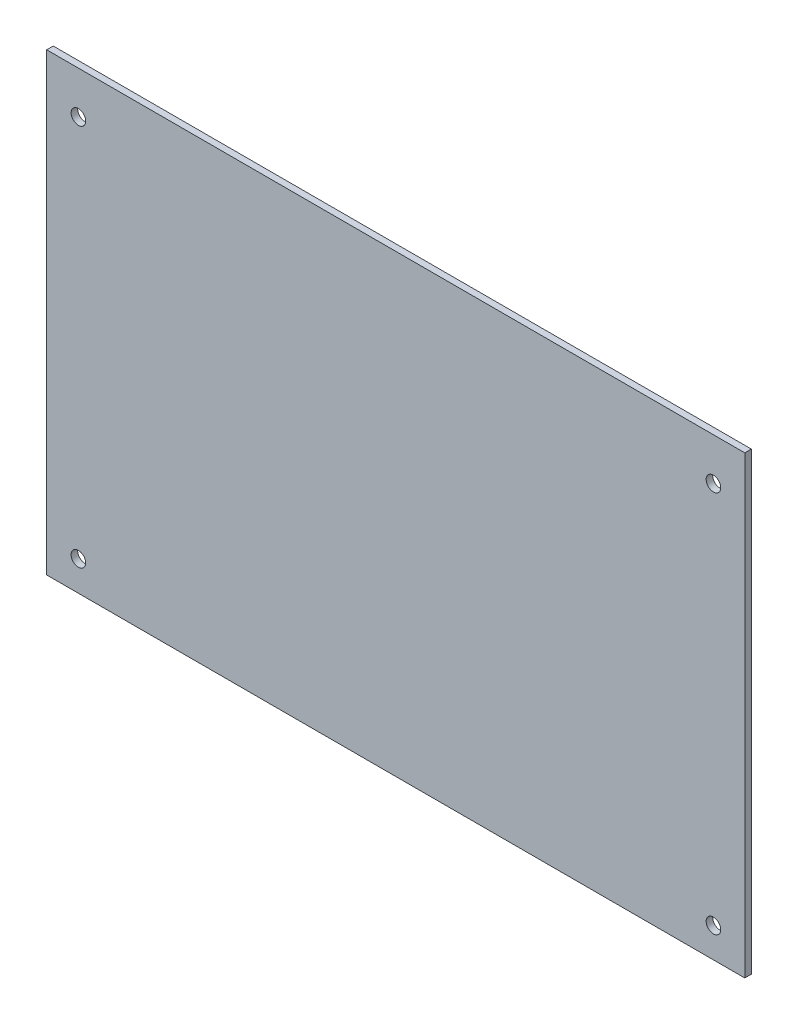
SolidWorks part; units mm, degrees
ref_plane "Front" through (0, 0, 0) normal (0, 0, 1) x (1, 0, 0)
ref_plane "Top" through (0, 0, 0) normal (0, 1, 0) x (1, 0, 0)
ref_plane "Right" through (0, 0, 0) normal (1, 0, 0) x (0, 0, -1)
sketch "Sketch1" plane through (0, 0, 0) normal (0, 0, 1) x (1, 0, 0)
  line L1 (-37.4747, 71.5987) -> (130.1653, 71.5987)
  line L2 (-37.4747, 71.5987) -> (-37.4747, -37.6213)
  line L3 (-37.4747, -37.6213) -> (130.1653, -37.6213)
  line L4 (130.1653, 71.5987) -> (130.1653, -37.6213)
  dimension "D1" = 167.64
  dimension "D2" = 109.22
extrude "PCB" add sketch "Sketch1" along normal blind 1.5748
sketch "Sketch2" plane through (0, 0, 1.5748) normal (0, 0, 1) x (1, 0, 0)
  line L0 (-37.4747, 71.5987) -> (-37.4747, -37.6213) construction
  line L1 (130.1653, 71.5987) -> (-37.4747, 71.5987) construction
  circle A0 centre (-29.8547, 61.4387) radius 1.75
  dimension "D1" = 3.5
  dimension "D2" = 7.62
  dimension "D3" = 10.16
extrude "mount hole cut" cut sketch "Sketch2" against normal blind 1.5748
pattern_linear "LPattern1" count 2 spacing 152.5 along (1, 0, 0) count 2 spacing 91.9 along (0, -1, 0) of "mount hole cut"
sketch "Sketch3" plane through (0, 0, 0) normal (0, 0, -1) x (-1, 0, 0)
  line L0 (11.0863, -1.9913) -> (3.6231, -1.9913) construction
  line L1 (3.6231, 1.0732) -> (11.0863, 1.0732)
  line L2 (3.6231, 1.0732) -> (3.6231, -5.0559)
  line L3 (3.6231, -5.0559) -> (11.0863, -5.0559)
  line L4 (11.0863, 1.0732) -> (11.0863, -5.0559)
  line L5 (7.3547, 1.0732) -> (7.3547, -5.0559) construction
  circle A1 centre (29.8547, 61.4387) radius 1.75 construction
  point P8 (7.3547, -1.9913)
  dimension "D1" = 22.5
  dimension "D2" = 63.43
extrude "Extrude1" add sketch "Sketch3" along normal blind 3.75
